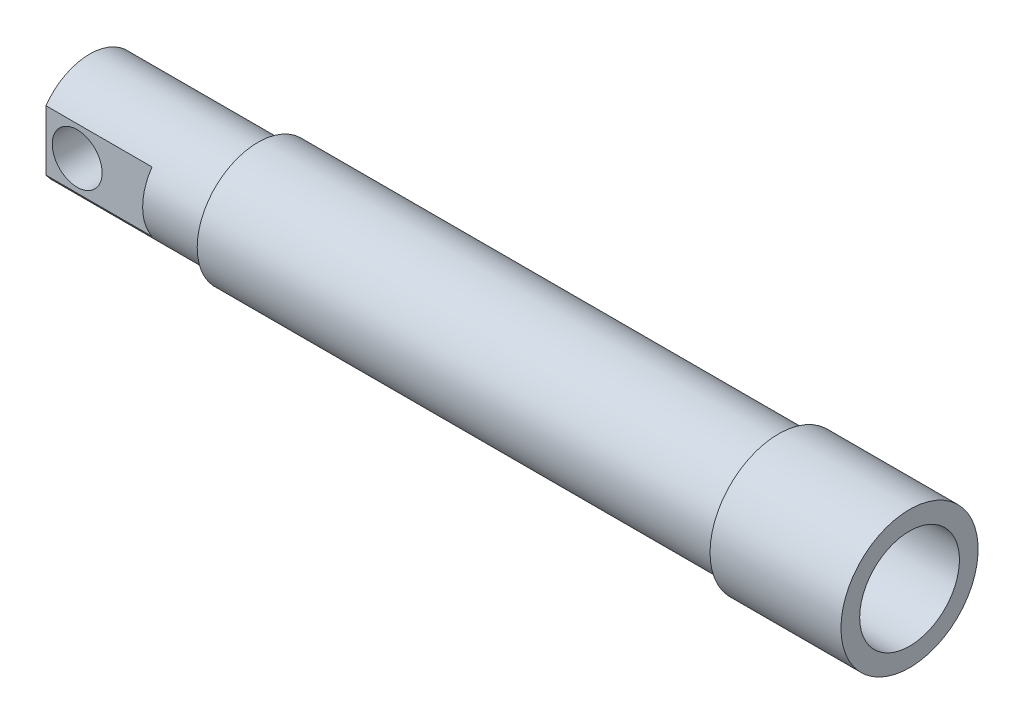
SolidWorks part; units mm, degrees
material "Alloy Steel"
ref_plane "Front Plane" through (0, 0, 0) normal (0, 0, 1) x (1, 0, 0)
ref_plane "Top Plane" through (0, 0, 0) normal (0, 1, 0) x (1, 0, 0)
ref_plane "Right Plane" through (0, 0, 0) normal (1, 0, 0) x (0, 0, -1)
sketch "Sketch1" plane through (0, 0, 0) normal (0, 0, 1) x (1, 0, 0)
  line L0 (-165.8938, 0) -> (165.8938, 0) construction
  line L1 (165.8938, 0) -> (165.8938, 34.925) construction
  line L2 (165.8938, 34.925) -> (99.2188, 34.925)
  line L3 (99.2188, 34.925) -> (99.2188, 30.9563)
  line L4 (99.2188, 30.9563) -> (-165.8938, 30.9562)
  line L5 (-165.8938, 30.9562) -> (-165.8938, 0) construction
  line L6 (-165.8938, 25.4) -> (165.8938, 25.4)
  line L7 (-165.8938, 30.9562) -> (-165.8938, 25.4)
  line L8 (165.8938, 34.925) -> (165.8938, 25.4)
  dimension "D1" = 331.7875
  dimension "D2" = 34.925
  dimension "D3" = 30.9562
  dimension "D4" = 66.675
  dimension "D5" = 25.4
revolve "Revolve1" add sketch "Sketch1" angle 360 about L0
sketch "Sketch2" plane through (-165.8938, 0, 0) normal (-1, 0, 0) x (0, 0, 1)
  circle A0 centre (0, 0) radius 26.9875
  dimension "D1" = 53.975
extrude "Boss-Extrude1" add sketch "Sketch2" along normal blind 85.725
sketch "Sketch3" plane through (-251.6188, 0, 0) normal (-1, 0, 0) x (0, 0, 1)
  line L0 (-22.225, 15.3093) -> (-22.225, -15.3093)
  line L1 (22.225, 15.3093) -> (22.225, -15.3093)
  line L2 (0, 26.9875) -> (0, -26.9875) construction
  arc A0 (-22.225, 15.3093) -> (-22.225, -15.3093) centre (0, 0) ccw
  arc A1 (22.225, -15.3093) -> (22.225, 15.3093) centre (0, 0) ccw
  circle A2 centre (0, 0) radius 26.9875 construction
  circle A3 centre (0, 0) radius 26.9875 construction
  dimension "D1" = 53.975
  dimension "D2" = 22.225
extrude "Cut-Extrude1" cut sketch "Sketch3" against normal blind 53.975
sketch "Sketch4" plane through (0, 0, 22.225) normal (0, 0, 1) x (1, 0, 0)
  line L0 (-197.6438, 0) -> (-251.6188, 0) construction
  line L1 (-197.6438, 15.3093) -> (-197.6438, -15.3093) construction
  line L2 (-251.6188, 15.3093) -> (-251.6188, -15.3093) construction
  circle A0 centre (-235.7438, 0) radius 12.7
  dimension "D1" = 25.4
  dimension "D2" = 15.875
extrude "Cut-Extrude2" cut sketch "Sketch4" against normal through all
ref_plane "Plane1" through (0, 0, -26.9875) normal (0, 0, -1) x (-1, 0, 0)
sketch "Sketch5" plane through (0, 0, -26.9875) normal (0, 0, -1) x (-1, 0, 0)
  line L0 (0, 0) -> (251.6187, 0) construction
  line L1 (251.6188, 15.3093) -> (251.6188, -15.3093) construction
  point P5 (181.7688, 0)
  dimension "D1" = 69.85
hole_wizard "1/4 NPT Tapped Hole1" positions "Sketch7" profile "Sketch6" size "1/4" standard "ANSI Inch"
sketch "Sketch7" plane through (0, 0, -26.9875) normal (0, 0, -1) x (-1, 0, 0)
  point P0 (181.7688, 0)
sketch "Sketch6" plane through (-181.7688, 0, -26.9875) normal (1, 0, 0) x (0, 1, 0)
  line L0 (0, 0) -> (0, 20.4111)
  line L1 (5.5626, 17.0688) -> (0, 20.4111)
  line L2 (-5.5626, 17.0688) -> (0, 20.4111) construction
  line L3 (5.5626, 17.0688) -> (5.5626, 10.0203)
  line L4 (5.5626, 10.0203) -> (6.558, 10.0203)
  line L5 (6.558, 10.0203) -> (6.858, 0)
  line L6 (-6.558, 10.0203) -> (-6.858, 0) construction
  line L7 (6.858, 0) -> (0, 0)
  line L8 (0, -6.35) -> (0, 107.95) construction
  line L11 (-5.5626, 10.0203) -> (-6.558, 10.0203) construction
  dimension "Tap Drill Dia." = 11.1252
  dimension "Tap Drill Depth" = 17.0688
  dimension "Thread Dia." = 13.716
  dimension "Thread Angle" = 3.43
  dimension "Thread Depth" = 10.0203
  dimension "Drill Angle" = 118
sketch "Sketch8" plane through (-165.8938, 0, 0) normal (1, 0, 0) x (0, 0, -1)
  circle A0 centre (0, 0) radius 12.7
  dimension "D1" = 25.4
extrude "Cut-Extrude3" cut sketch "Sketch8" against normal blind 26.9875
